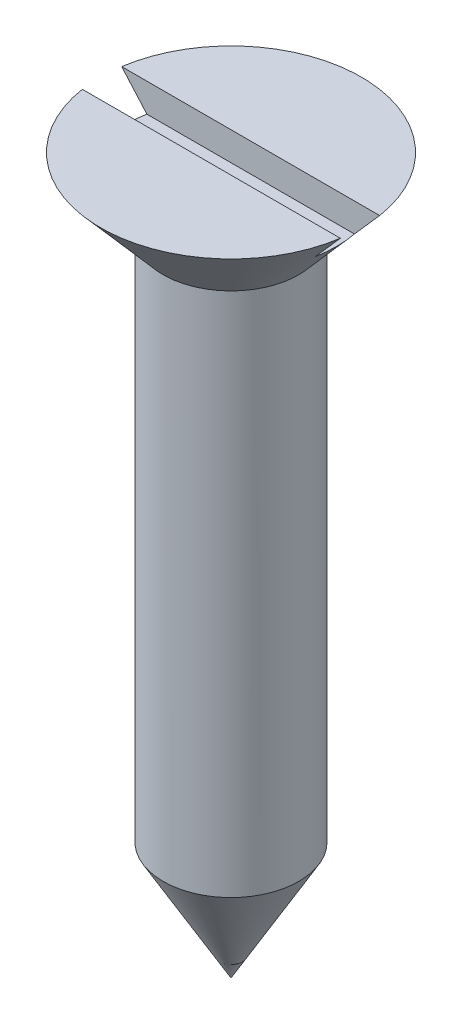
SolidWorks part; units mm, degrees
ref_plane "Front Plane" through (0, 0, 0) normal (0, 0, 1) x (1, 0, 0)
ref_plane "Top Plane" through (0, 0, 0) normal (0, 1, 0) x (1, 0, 0)
ref_plane "Right Plane" through (0, 0, 0) normal (1, 0, 0) x (0, 0, -1)
sketch "Sketch1" plane through (0, 0, 0) normal (0, 1, 0) x (1, 0, 0)
  circle A0 centre (0, 0) radius 2.413
  dimension "D1" = 4.826
extrude "Boss-Extrude1" add sketch "Sketch1" along normal blind 25.4
sketch "Sketch2" plane through (0, 0, 0) normal (0, 0, 1) x (1, 0, 0)
  line L0 (0, 25.4) -> (4.6355, 25.4)
  line L1 (2.413, 25.4) -> (-2.413, 25.4) construction
  line L2 (4.6355, 25.4) -> (0, 20.0675)
  line L3 (0, 20.0675) -> (0, 25.4)
  line L4 (0, 20.0675) -> (0, 32.0501) construction
  dimension "D1" = 4.6355
  dimension "D2" = 49
revolve "Revolve1" add sketch "Sketch2" angle 360 about L4
sketch "Sketch3" plane through (0, 0, 0) normal (0, 0, 1) x (1, 0, 0)
  line L0 (0, 0) -> (2.413, 4.1794)
  line L1 (2.413, 0) -> (2.413, 22.8433) construction
  line L2 (2.413, 4.1794) -> (2.413, 0)
  line L3 (2.413, 0) -> (0, 0)
  line L4 (0, 4.3852) -> (0, 1.0909) construction
  line L5 (2.413, 0) -> (2.413, -0.635)
  line L6 (2.413, -0.635) -> (0, -0.635)
  line L7 (0, -0.635) -> (0, 0)
  dimension "D1" = 30
  dimension "D2" = 0.635
revolve "Cut-Revolve1" cut sketch "Sketch3" angle 360 about L4
sketch "Sketch4" plane through (0, 25.4, 0) normal (0, 1, 0) x (1, 0, 0)
  line L1 (7.0873, -0.6985) -> (-7.0873, -0.6985)
  line L2 (7.0873, -0.6985) -> (7.0873, 0.6985)
  line L3 (7.0873, 0.6985) -> (-7.0873, 0.6985)
  line L4 (-7.0873, -0.6985) -> (-7.0873, 0.6985)
  line L5 (7.0873, -0.6985) -> (-7.0873, 0.6985) construction
  line L6 (7.0873, 0.6985) -> (-7.0873, -0.6985) construction
  point P0 (0, 0)
  dimension "D1" = 1.397
extrude "Cut-Extrude1" cut sketch "Sketch4" against normal blind 1.016 contours L4 L3 L2 L1
